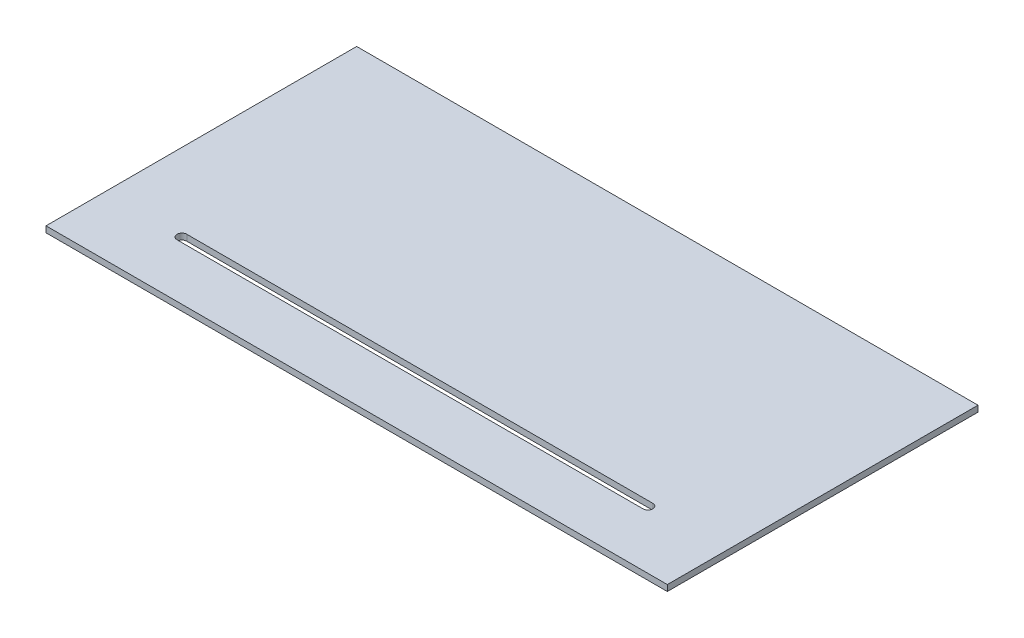
SolidWorks part; units mm, degrees
material "Cedar"
ref_plane "Front Plane" through (0, 0, 0) normal (0, 0, 1) x (1, 0, 0)
ref_plane "Top Plane" through (0, 0, 0) normal (0, 1, 0) x (1, 0, 0)
ref_plane "Right Plane" through (0, 0, 0) normal (1, 0, 0) x (0, 0, -1)
sketch "Sketch1" plane through (0, 0, 0) normal (0, 1, 0) x (1, 0, 0)
  line L1 (-609.6, -304.8) -> (609.6, -304.8)
  line L2 (-609.6, -304.8) -> (-609.6, 304.8)
  line L3 (-609.6, 304.8) -> (609.6, 304.8)
  line L4 (609.6, -304.8) -> (609.6, 304.8)
  line L5 (-609.6, -304.8) -> (609.6, 304.8) construction
  line L6 (-609.6, 304.8) -> (609.6, -304.8) construction
  point P0 (0, 0)
  dimension "D1" = 1219.2
  dimension "D2" = 609.6
extrude "Boss-Extrude1" add sketch "Sketch1" along normal blind 11.9062
sketch "Sketch2" plane through (0, 11.9062, 0) normal (0, 1, 0) x (1, 0, 0)
  line L0 (-457.2, -190.5) -> (457.2, -190.5) construction
  line L1 (-457.2, -180.975) -> (457.2, -180.975)
  line L2 (-457.2, -200.025) -> (457.2, -200.025)
  line L3 (0, -190.5) -> (0, 0) construction
  line L4 (-609.6, -304.8) -> (609.6, -304.8) construction
  arc A0 (-457.2, -180.975) -> (-457.2, -200.025) centre (-457.2, -190.5) ccw
  arc A1 (457.2, -200.025) -> (457.2, -180.975) centre (457.2, -190.5) ccw
  point P2 (0, -190.5)
  dimension "D1" = 19.05
  dimension "D2" = 914.4
  dimension "D3" = 114.3
extrude "Cut-Extrude1" cut sketch "Sketch2" against normal through all
